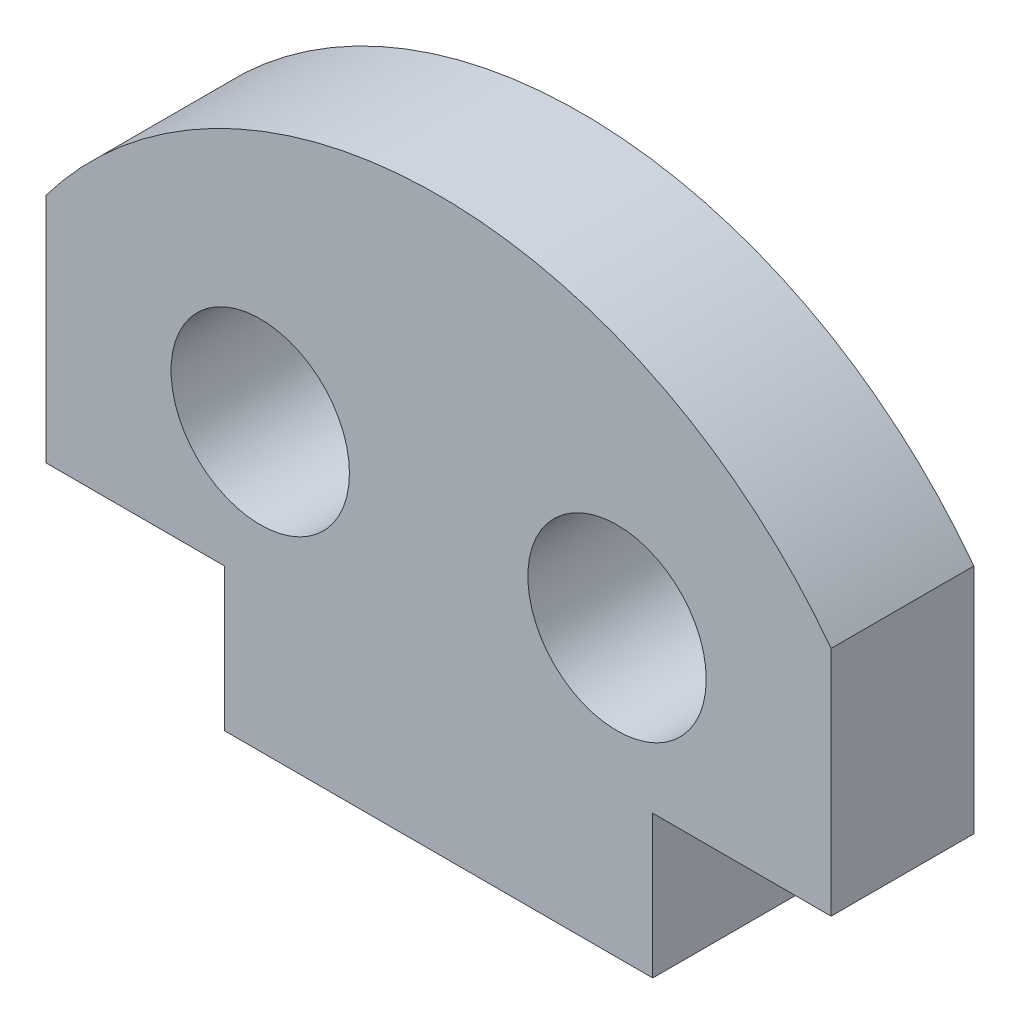
SolidWorks part; units mm, degrees
ref_plane "Front Plane" through (0, 0, 0) normal (0, 0, 1) x (1, 0, 0)
ref_plane "Top Plane" through (0, 0, 0) normal (0, 1, 0) x (1, 0, 0)
ref_plane "Right Plane" through (0, 0, 0) normal (1, 0, 0) x (0, 0, -1)
sketch "Model" plane through (0, 0, 0) normal (0, 0, 1) x (1, 0, 0)
  line L0 (1953.6768, 1458.8841) -> (1951.1768, 1458.8841)
  line L1 (1951.1768, 1458.8841) -> (1951.1768, 1462.1341)
  line L2 (1962.1768, 1458.8841) -> (1962.1768, 1462.1341)
  line L3 (1962.1768, 1458.8841) -> (1959.6768, 1458.8841)
  line L4 (1953.6768, 1458.8841) -> (1953.6768, 1456.8841)
  line L5 (1953.6768, 1456.8841) -> (1959.6768, 1456.8841)
  line L6 (1959.6768, 1456.8841) -> (1959.6768, 1458.8841)
  arc A0 (1962.1768, 1462.1341) -> (1951.1768, 1462.1341) centre (1956.6768, 1458.0091) ccw
  circle A81 centre (1959.1768, 1460.8841) radius 1.25
  circle A82 centre (1954.1768, 1460.8841) radius 1.25
  dimension "D5" = 1954.1768
  dimension "D6" = 1956.6768
  dimension "D7" = 1959.1768
  dimension "D1" = 2.5
  dimension "D2" = 6.875
  dimension "D3" = 1951.1768
  dimension "D4" = 1953.6768
  dimension "D8" = 1456.8841
  dimension "D9" = 1458.0091
  dimension "D10" = 1458.8841
  dimension "D11" = 1460.8841
extrude "Boss-Extrude1" add sketch "Model" along normal blind 2
